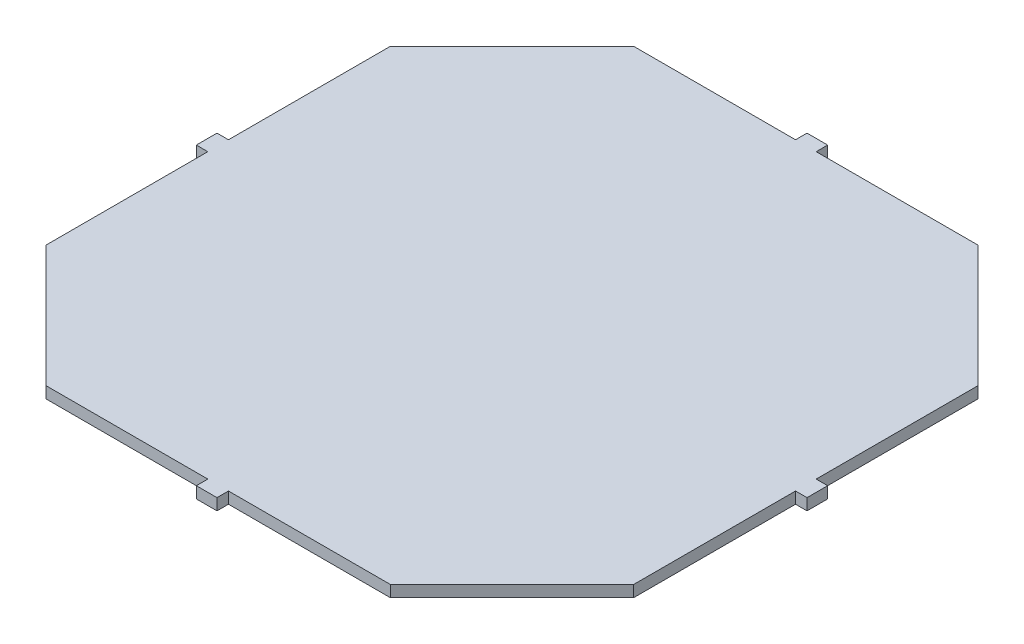
SolidWorks part; units mm, degrees
material "Acrylic (Medium-high impact)"
ref_plane "Front Plane" through (0, 0, 0) normal (0, 0, 1) x (1, 0, 0)
ref_plane "Top Plane" through (0, 0, 0) normal (0, 1, 0) x (1, 0, 0)
ref_plane "Right Plane" through (0, 0, 0) normal (1, 0, 0) x (0, 0, -1)
sketch "Sketch1" plane through (0, 0, 0) normal (0, 1, 0) x (1, 0, 0)
  line L0 (-25.6066, 15) -> (-15, 25.6066)
  line L1 (-15, -25.6066) -> (15, -25.6066)
  line L2 (-25.6066, -15) -> (-25.6066, 15)
  line L3 (-15, 25.6066) -> (15, 25.6066)
  line L4 (25.6066, -15) -> (25.6066, 15)
  line L5 (-20.3033, -20.3033) -> (20.3033, 20.3033) construction
  line L6 (-20.3033, 20.3033) -> (20.3033, -20.3033) construction
  line L7 (-25.6066, -15) -> (-15, -25.6066)
  line L8 (15, -25.6066) -> (25.6066, -15)
  line L9 (15, 25.6066) -> (25.6066, 15)
  point P0 (0, 0)
  dimension "D1" = 30
  dimension "D2" = 30
  dimension "D3" = 135
  dimension "D4" = 135
  dimension "D5" = 15
  dimension "D6" = 135
extrude "Boss-Extrude1" add sketch "Sketch1" along normal blind 1
sketch "Sketch2" plane through (0, 1, 0) normal (0, 1, 0) x (1, 0, 0)
  line L0 (0, 25.6066) -> (0, -25.6066) construction
  line L1 (15, 25.6066) -> (-15, 25.6066) construction
  line L2 (-15, -25.6066) -> (15, -25.6066) construction
  line L3 (-25.6066, 0) -> (25.6066, 0) construction
  line L4 (-25.6066, 15) -> (-25.6066, -15) construction
  line L5 (25.6066, -15) -> (25.6066, 15) construction
  line L6 (-25.6066, 0.9) -> (-26.6066, 0.9)
  line L7 (-26.6066, 0.9) -> (-26.6066, -0.9)
  line L8 (-26.6066, -0.9) -> (-25.6066, -0.9)
  line L9 (-0.9, 25.6066) -> (-0.9, 26.6066)
  line L10 (-0.9, 26.6066) -> (0.9, 26.6066)
  line L11 (0.9, 26.6066) -> (0.9, 25.6066)
  line L12 (0.9, -26.6066) -> (0.9, -25.6066)
  line L13 (-0.9, -26.6066) -> (0.9, -26.6066)
  line L14 (-0.9, -25.6066) -> (-0.9, -26.6066)
  line L15 (26.6066, -0.9) -> (25.6066, -0.9)
  line L16 (26.6066, 0.9) -> (26.6066, -0.9)
  line L17 (25.6066, 0.9) -> (26.6066, 0.9)
  line L18 (-0.9, 25.6066) -> (0.9, 25.6066)
  line L19 (25.6066, 0.9) -> (25.6066, -0.9)
  line L20 (-0.9, -25.6066) -> (0.9, -25.6066)
  line L21 (-25.6066, -0.9) -> (-25.6066, 0.9)
  dimension "D1" = 1.8
  dimension "D2" = 1
  dimension "D3" = 1.8
  dimension "D4" = 1
extrude "Boss-Extrude2" add sketch "Sketch2" against normal blind 1
